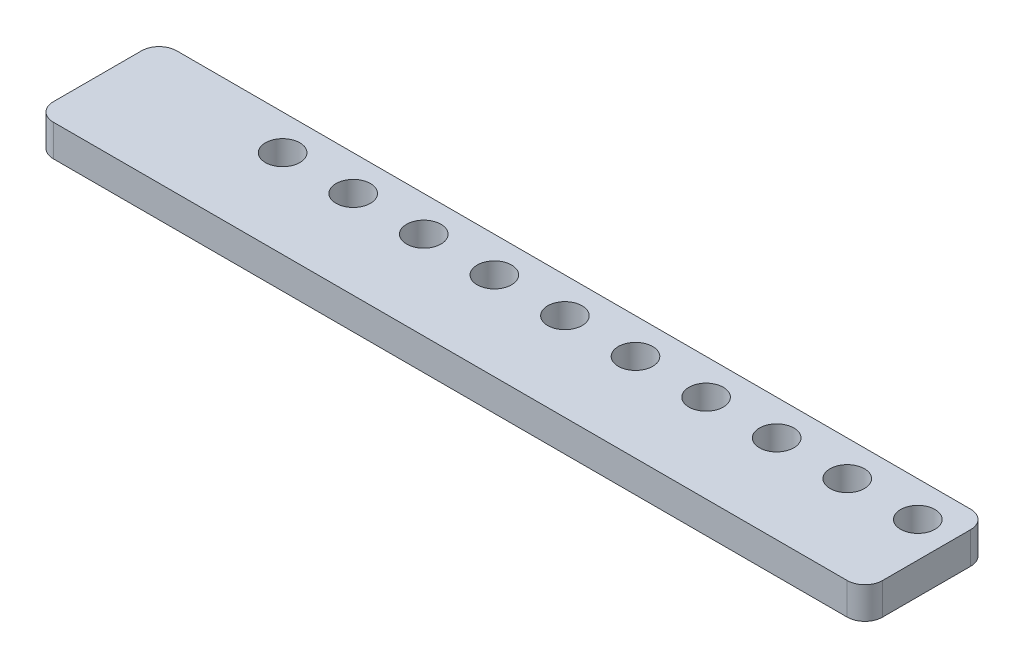
SolidWorks part; units mm, degrees
ref_plane "Front Plane" through (0, 0, 0) normal (0, 0, 1) x (1, 0, 0)
ref_plane "Top Plane" through (0, 0, 0) normal (0, 1, 0) x (1, 0, 0)
ref_plane "Right Plane" through (0, 0, 0) normal (1, 0, 0) x (0, 0, -1)
sketch "Sketch1" plane through (0, 0, 0) normal (0, 1, 0) x (1, 0, 0)
  line L1 (2, 0) -> (92, 0)
  line L2 (0, -2) -> (0, -12)
  line L3 (2, -14) -> (92, -14)
  line L4 (94, -2) -> (94, -12)
  arc A0 (92, -14) -> (94, -12) centre (92, -12) ccw
  arc A1 (0, -12) -> (2, -14) centre (2, -12) ccw
  arc A2 (2, 0) -> (0, -2) centre (2, -2) ccw
  arc A3 (92, 0) -> (94, -2) centre (92, -2) cw
  point P7 (94, -14)
  point P12 (0, 0)
  point P15 (94, 0)
  dimension "D3" = 2
  dimension "D1" = 94
  dimension "D2" = 14
extrude "Boss-Extrude1" add sketch "Sketch1" along normal blind 3.6
sketch "Sketch2" plane through (0, 3.6, 0) normal (0, 1, 0) x (1, 0, 0)
  line L1 (94, -12) -> (94, -2) construction
  line L2 (90, -4) -> (0, -4) construction
  line L3 (0, -2) -> (0, -12) construction
  line L4 (92, 0) -> (2, 0) construction
  circle A0 centre (90, -4) radius 1.95
  circle A1 centre (82, -4) radius 1.95
  circle A2 centre (18, -4) radius 1.95
  circle A3 centre (26, -4) radius 1.95
  circle A4 centre (34, -4) radius 1.95
  circle A5 centre (42, -4) radius 1.95
  circle A6 centre (50, -4) radius 1.95
  circle A7 centre (58, -4) radius 1.95
  circle A8 centre (66, -4) radius 1.95
  circle A9 centre (74, -4) radius 1.95
  dimension "D1" = 3.9
  dimension "D4" = 3.9
  dimension "D7" = 3.9
  dimension "D8" = 3.9
  dimension "D9" = 3.9
  dimension "D10" = 3.9
  dimension "D11" = 3.9
  dimension "D12" = 3.9
  dimension "D13" = 3.9
  dimension "D14" = 3.9
  dimension "D3" = 4
  dimension "D5" = 8
  dimension "D6" = 18
  dimension "D15" = 8
  dimension "D16" = 8
  dimension "D17" = 8
  dimension "D18" = 8
  dimension "D19" = 8
  dimension "D20" = 8
  dimension "D21" = 8
  dimension "D22" = 4
extrude "Cut-Extrude1" cut sketch "Sketch2" against normal blind 3.6
